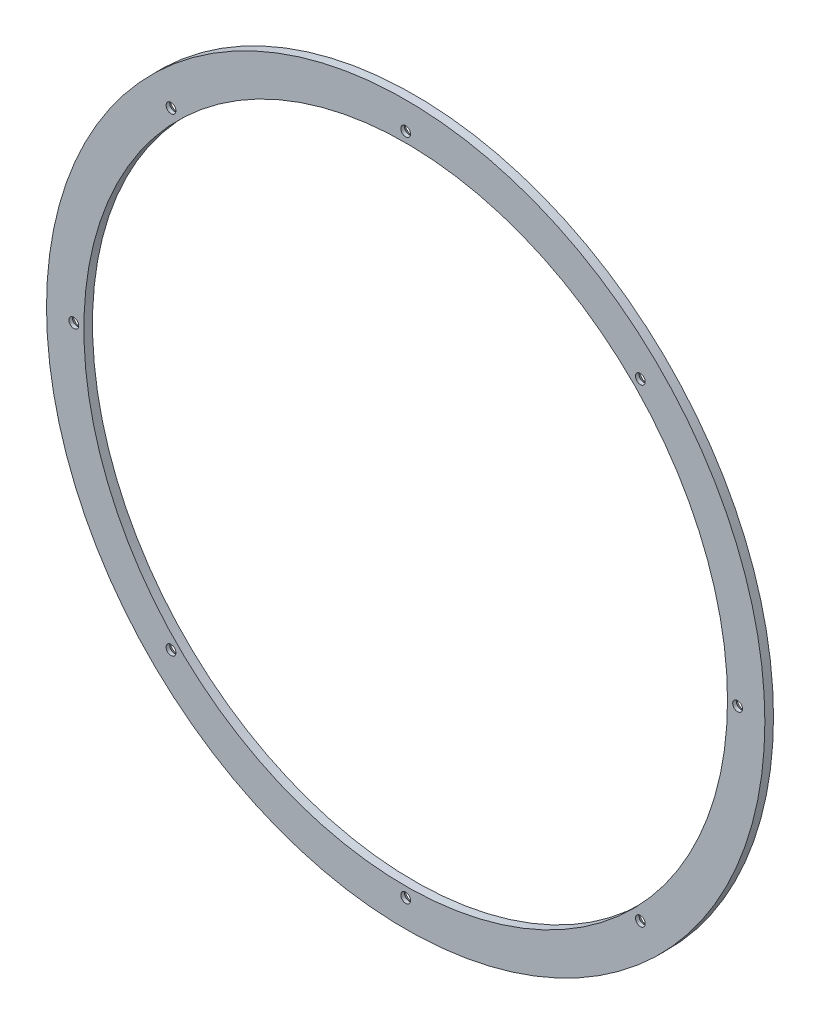
SolidWorks part; units mm, degrees
material "3.3315 (EN-AW 5005)"
ref_plane "Front Plane" through (0, 0, 0) normal (0, 0, 1) x (1, 0, 0)
ref_plane "Top Plane" through (0, 0, 0) normal (0, 1, 0) x (1, 0, 0)
ref_plane "Right Plane" through (0, 0, 0) normal (1, 0, 0) x (0, 0, -1)
sketch "Sketch1" plane through (0, 0, 0) normal (0, 0, 1) x (1, 0, 0)
  circle A0 centre (0, 0) radius 125
  circle A1 centre (0, 0) radius 112
  dimension "D1" = 224
  dimension "D2" = 250
extrude "Boss-Extrude1" add sketch "Sketch1" along normal blind 3
hole_wizard "CSK for M3 Countersunk Flat Head Screw1" positions "Sketch2" profile "Sketch3" countersink size "M3" standard "ISO" end condition through all
sketch "Sketch2" plane through (0, 0, 0) normal (0, 0, -1) x (-1, 0, 0)
  line L0 (115.5, 0) -> (0, 0) construction
  point P0 (115.5, 0)
  dimension "D1" = 115.5
sketch "Sketch3" plane through (-115.5, 0, 0) normal (1, 0, 0) x (0, 1, 0)
  line L0 (0, 0) -> (0, 3)
  line L1 (0, 3) -> (1.7, 3)
  line L2 (1.7, 3) -> (1.7, 1.75)
  line L3 (1.7, 1.75) -> (3.45, 0)
  line L5 (3.45, 0) -> (0, 0)
  line L6 (-1.7, 1.75) -> (-3.45, 0) construction
  line L11 (0, -6.35) -> (0, 107.95) construction
  dimension "Thru Hole Dia." = 3.4
  dimension "Thru Hole Depth" = 3
  dimension "Near C'Sink Dia." = 6.9
  dimension "Near C'Sink Angle" = 90
pattern_circular "CirPattern1" count 8 over 360 about axis through (0, 0, 0) along (0, 0, 1) of "CSK for M3 Countersunk Flat Head Screw1"
